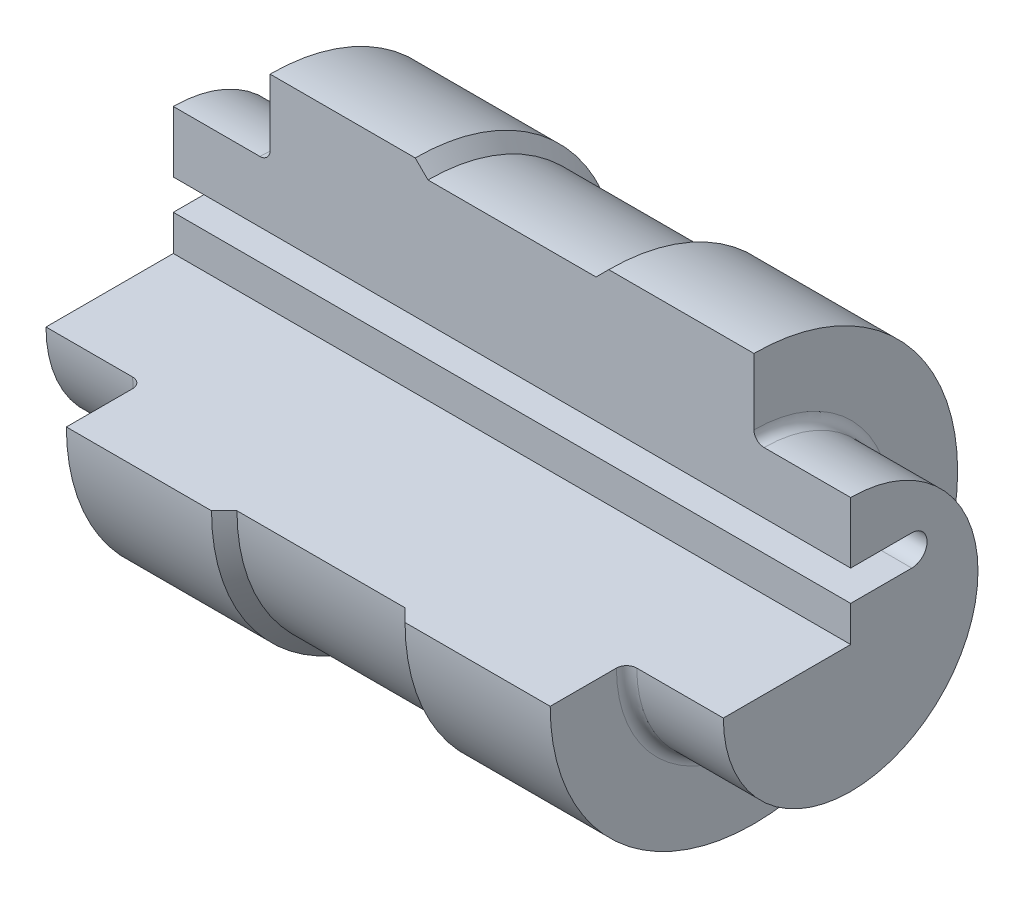
SolidWorks part; units mm, degrees
material "AISI 1020"
ref_plane "Płaszczyzna przednia" through (0, 0, 0) normal (0, 0, 1) x (1, 0, 0)
ref_plane "Płaszczyzna górna" through (0, 0, 0) normal (0, 1, 0) x (1, 0, 0)
ref_plane "Płaszczyzna prawa" through (0, 0, 0) normal (1, 0, 0) x (0, 0, -1)
sketch "Szkic2" plane through (0, 0, 0) normal (0, 0, 1) x (1, 0, 0)
  line L0 (0, 0) -> (0, 25)
  line L1 (0, 25) -> (19, 25)
  line L2 (19, 25) -> (19, 40)
  line L3 (19, 40) -> (47.5, 40)
  line L4 (47.5, 40) -> (50, 37.5)
  line L5 (50, 37.5) -> (83, 37.5)
  line L6 (83, 37.5) -> (85.5, 40)
  line L7 (85.5, 40) -> (114, 40)
  line L8 (114, 40) -> (114, 25)
  line L9 (114, 25) -> (133, 25)
  line L10 (133, 25) -> (133, 0)
  line L11 (133, 0) -> (0, 0)
  dimension "D1" = 25
  dimension "D2" = 40
  dimension "D3" = 135
  dimension "D4" = 135
  dimension "D5" = 19
  dimension "D6" = 28.5
  dimension "D7" = 133
  dimension "D8" = 19
  dimension "D9" = 2.5
revolve "Obrót1" add sketch "Szkic2" angle 360 about L11
fillet "Zaokrąglenie1" radius 2 2 edges at (19, 25, 0) (114, 25, 0)
sketch "Szkic3" plane through (0, 0, 0) normal (-1, 0, 0) x (0, 0, 1)
  line L0 (0, 0) -> (0, 7)
  line L1 (0, 7) -> (-12, 7)
  line L2 (-12, 13) -> (0, 13)
  line L3 (0, 13) -> (0, 40)
  line L4 (40, 0) -> (0, 0)
  arc A0 (-12, 7) -> (-12, 13) centre (-12, 10) cw
  circle A1 centre (0, 0) radius 40 construction
  arc A2 (0, 40) -> (40, 0) centre (0, 0) cw
  dimension "D2" = 3
  dimension "D1" = 12
  dimension "D3" = 7
extrude "Wytnij-wyciągnięcie1" cut sketch "Szkic3" against normal through all
equation "\"B\" = 19"
equation "\"C\" = 28.5"
equation "\"A\"= 133"
